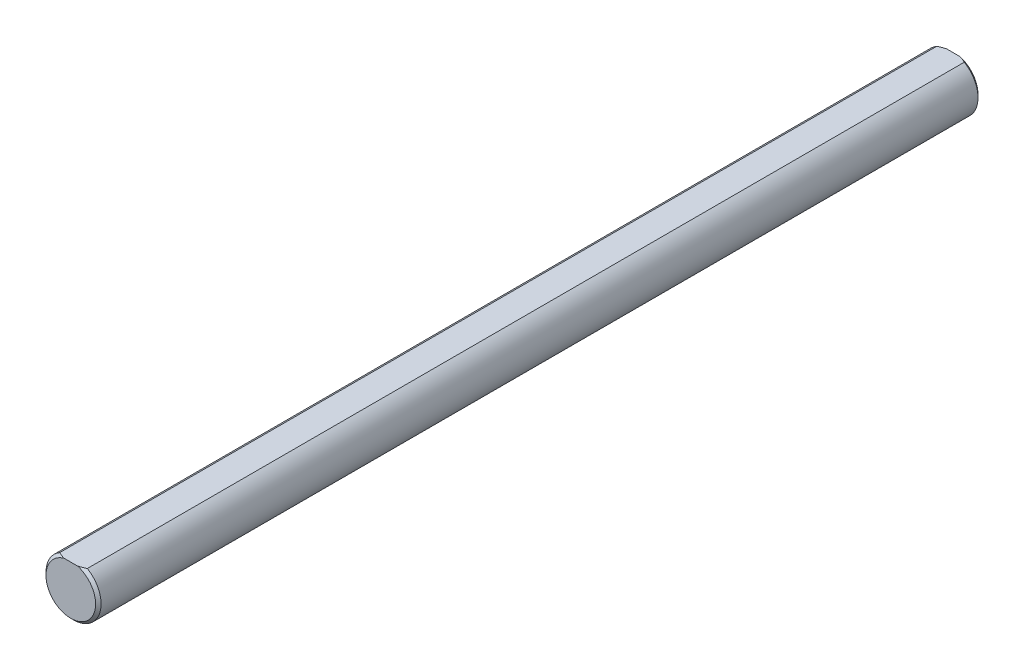
SolidWorks part; units mm, degrees
ref_plane "Front Plane" through (0, 0, 0) normal (0, 0, 1) x (1, 0, 0)
ref_plane "Top Plane" through (0, 0, 0) normal (0, 1, 0) x (1, 0, 0)
ref_plane "Right Plane" through (0, 0, 0) normal (1, 0, 0) x (0, 0, -1)
sketch "Sketch1" plane through (0, 0, 0) normal (0, 0, 1) x (1, 0, 0)
  line L0 (-2.3813, 4.1244) -> (2.3813, 4.1244) construction
  circle A1 centre (0, 0) radius 4.7625 construction
  dimension "Diameter" = 9.525
  dimension "Flat Width" = 4.7625
sketch "Sketch2" plane through (0, 0, 0) normal (1, 0, 0) x (0, 0, -1)
  line L0 (-76.2, 4.7625) -> (76.2, 4.7625) construction
  line L1 (0, 4.7625) -> (0, -4.7625) construction
  line L2 (0, 4.7625) -> (0, -4.7625) construction
  line L3 (-76.2, 4.7625) -> (-76.2, -4.7625) construction
  line L4 (-76.2, -4.7625) -> (76.2, -4.7625) construction
  point P2 (0, 4.7625)
  point P3 (57.15, 4.7625)
  point P4 (-57.15, 4.7625)
  dimension "Length" = 152.4
  dimension "D2" = 19.05
  dimension "D1" = 19.05
  dimension "D-Profile Length" = 152.4
sketch "Sketch3" plane through (0, 0, 0) normal (0, 0, 1) x (1, 0, 0)
  circle A1 centre (0, 0) radius 4.7625 construction
  circle A3 centre (0, 0) radius 4.7625
extrude "Boss-Extrude2" add sketch "Sketch3" along normal up to vertex (76.2 mm away) and the other way up to vertex (76.2 mm away) up to point (0, 4.7625, 76.2) other way up to point (0, 4.7625, -76.2)
sketch "Sketch10" plane through (0, 0, 0) normal (0, 0, 1) x (1, 0, 0)
  line L0 (-2.3813, 4.1244) -> (2.3813, 4.1244)
  line L1 (0, 0) -> (0, 4.7625) construction
  circle A0 centre (0, 0) radius 4.7625 construction
  circle A1 centre (0, 0) radius 4.7625 construction
  arc A2 (-2.3813, 4.1244) -> (2.3813, 4.1244) centre (0, 0) cw
extrude "Cut-Extrude5" cut sketch "Sketch10" against normal through all both and the other way through all
chamfer "Chamfer1" distance 0.4762 angle 45 4 edges at (0, -4.7625, 76.2) (0, -4.7625, -76.2) (0, 4.1244, -76.2) (0, 4.1244, 76.2)
equation "\"D1@Chamfer1\"= \"Diameter@Sketch1\" / 20"
equation "\"D1@Sketch2\"=\"Diameter@Sketch1\"*2"
equation "\"D2@Sketch2\"=\"D1@Sketch2\""
